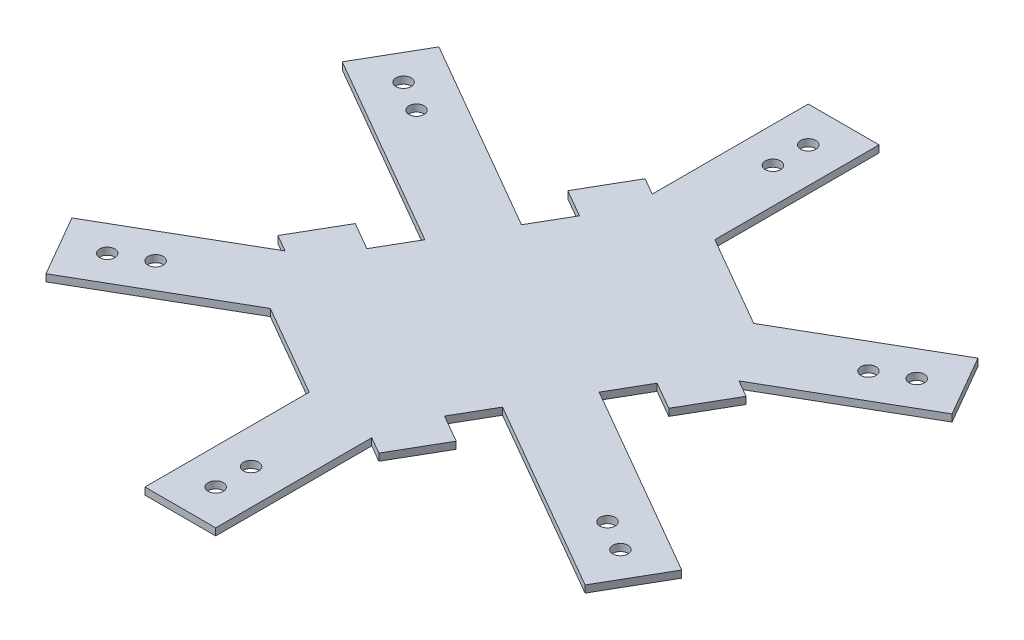
SolidWorks part; units mm, degrees
material "Thornel Mat VMA"
ref_plane "Front Plane" through (0, 0, 0) normal (0, 0, 1) x (1, 0, 0)
ref_plane "Top Plane" through (0, 0, 0) normal (0, 1, 0) x (1, 0, 0)
ref_plane "Right Plane" through (0, 0, 0) normal (1, 0, 0) x (0, 0, -1)
sketch "Sketch1" plane through (0, 0, 0) normal (0, 1, 0) x (1, 0, 0)
  line L0 (0, 88.7676) -> (0, -88.7676) construction
  line L1 (102.5, 0) -> (51.25, 88.7676)
  line L2 (51.25, 88.7676) -> (-51.25, 88.7676)
  line L3 (-51.25, 88.7676) -> (-102.5, 0)
  line L4 (-102.5, 0) -> (-51.25, -88.7676)
  line L5 (-51.25, -88.7676) -> (51.25, -88.7676)
  line L6 (51.25, -88.7676) -> (102.5, 0)
  line L7 (73.6325, 0) -> (36.8162, 63.7676)
  line L8 (-10, 63.7676) -> (-36.8162, 63.7676)
  line L9 (-36.8162, 63.7676) -> (-73.6325, 0)
  line L10 (-73.6325, 0) -> (-36.8162, -63.7676)
  line L11 (10, -63.7676) -> (36.8162, -63.7676)
  line L12 (36.8162, -63.7676) -> (73.6325, 0)
  line L17 (-25, -40.75) -> (25, 40.75) construction
  line L18 (-25, 40.75) -> (25, -40.75) construction
  line L19 (-10, 63.7676) -> (-10, 45.7676)
  line L20 (-10, 45.7676) -> (-30, 45.7676)
  line L21 (-30, -45.7676) -> (-30, 45.7676)
  line L22 (-30, 0) -> (25, 0) construction
  line L23 (-10, -45.7676) -> (-30, -45.7676)
  line L24 (-10, -63.7676) -> (-10, -45.7676)
  line L25 (10, -63.7676) -> (10, -45.7676)
  line L26 (10, -45.7676) -> (30, -45.7676)
  line L27 (30, -45.7676) -> (30, 45.7676)
  line L28 (10, 45.7676) -> (30, 45.7676)
  line L29 (10, 63.7676) -> (10, 45.7676)
  line L30 (-36.8162, -63.7676) -> (-10, -63.7676)
  line L31 (10, 63.7676) -> (36.8162, 63.7676)
  circle A0 centre (0, 0) radius 88.7676 construction
  circle A1 centre (0, 0) radius 63.7676 construction
  dimension "D1" = 205
  dimension "D2" = 25
  dimension "D3" = 81.5
  dimension "D4" = 50
  dimension "D5" = 18
  dimension "D6" = 10
  dimension "D7" = 20
extrude "Boss-Extrude2" add sketch "Sketch1" along normal blind 2
sketch "Sketch2" plane through (0, 2, 0) normal (0, 1, 0) x (1, 0, 0)
  line L0 (-55.2244, -31.8838) -> (-76.875, -44.3838) construction
  line L1 (-73.6325, 0) -> (-36.8162, -63.7676) construction
  line L2 (-102.5, 0) -> (-51.25, -88.7676) construction
  line L3 (-55.2244, -31.8838) -> (-63.8846, -36.8838) construction
  line L4 (-63.8846, -36.8838) -> (-72.5449, -41.8838) construction
  circle A0 centre (-72.5449, -41.8838) radius 2.15
  circle A1 centre (-63.8846, -36.8838) radius 2.15
  circle A2 centre (-72.5449, 41.8838) radius 2.15
  circle A3 centre (-63.8846, 36.8838) radius 2.15
  circle A4 centre (0, 83.7676) radius 2.15
  circle A5 centre (0, 73.7676) radius 2.15
  circle A6 centre (72.5449, 41.8838) radius 2.15
  circle A7 centre (63.8846, 36.8838) radius 2.15
  circle A8 centre (72.5449, -41.8838) radius 2.15
  circle A9 centre (63.8846, -36.8838) radius 2.15
  circle A10 centre (0, -83.7676) radius 2.15
  circle A11 centre (0, -73.7676) radius 2.15
  point P33 (0, 0)
  dimension "D3" = 4.3
  dimension "D4" = 4.3
  dimension "D1" = 10
  dimension "D2" = 10
  dimension "D5" = 6
extrude "Cut-Extrude1" cut sketch "Sketch2" against normal blind 10
sketch "Sketch7" plane through (0, 0, 0) normal (0, -1, 0) x (1, 0, 0)
  line L1 (73.6325, 0) -> (36.8162, 63.7676)
  line L2 (36.8162, 63.7676) -> (-36.8162, 63.7676)
  line L3 (-36.8162, 63.7676) -> (-73.6325, 0)
  line L4 (-73.6325, 0) -> (-36.8162, -63.7676)
  line L5 (-36.8162, -63.7676) -> (36.8162, -63.7676)
  line L6 (36.8162, -63.7676) -> (73.6325, 0)
  circle A0 centre (0, 0) radius 63.7676 construction
extrude "Cut-Extrude3" cut sketch "Sketch7" against normal blind 30
sketch "Sketch8" plane through (0, 0, 0) normal (0, -1, 0) x (1, 0, 0)
  line L0 (-36.8162, 63.7676) -> (36.8162, -63.7676) construction
  line L1 (0, 0) -> (-23, 39.8372) construction
  line L2 (-23, 39.8372) -> (2.9808, 54.8372) construction
  line L3 (55.2244, 31.8838) -> (0, 0) construction
  line L4 (36.8162, 63.7676) -> (73.6325, 0) construction
  line L5 (-48.9808, 24.8372) -> (2.9808, 54.8372)
  line L6 (2.9808, 54.8372) -> (48.9808, -24.8372)
  line L7 (25.9808, 15) -> (0, 0)
  line L8 (-23, 39.8372) -> (0, 0)
  line L9 (-48.9808, 24.8372) -> (-2.9808, -54.8372)
  line L10 (-2.9808, -54.8372) -> (48.9808, -24.8372)
  point P16 (-25.9808, -15)
  dimension "D1" = 46
  dimension "D3" = 30
  dimension "D4" = 90
extrude "Boss-Extrude4" add sketch "Sketch8" against normal blind 2 separate body contours L5 L8 L7 L6 | L9 L10 L6 L7 L8 L5
sketch "Sketch9" plane through (0, 0, 0) normal (0, -1, 0) x (-1, 0, 0)
  line L0 (55.2244, -31.8838) -> (50.2244, -40.5441) construction
  line L1 (73.6325, 0) -> (36.8162, -63.7676) construction
  line L2 (55.2244, -31.8838) -> (60.2244, -23.2235) construction
  line L3 (60.2244, -23.2235) -> (25.5833, -3.2235)
  line L4 (76.875, -44.3838) -> (55.2244, -31.8838) construction
  line L5 (102.5, 0) -> (51.25, -88.7676) construction
  line L6 (50.2244, -40.5441) -> (15.5833, -20.5441)
  line L7 (60.2244, -23.2235) -> (50.2244, -40.5441)
  line L8 (25.5833, -3.2235) -> (15.5833, -20.5441)
  line L9 (-10, -63.7676) -> (-10, -23.7676)
  line L10 (10, -63.7676) -> (-10, -63.7676)
  line L11 (10, -63.7676) -> (10, -23.7676)
  line L12 (10, -23.7676) -> (-10, -23.7676)
  line L13 (-60.2244, -23.2235) -> (-25.5833, -3.2235)
  line L14 (-50.2244, -40.5441) -> (-60.2244, -23.2235)
  line L15 (-50.2244, -40.5441) -> (-15.5833, -20.5441)
  line L16 (-15.5833, -20.5441) -> (-25.5833, -3.2235)
  line L17 (-50.2244, 40.5441) -> (-15.5833, 20.5441)
  line L18 (-60.2244, 23.2235) -> (-50.2244, 40.5441)
  line L19 (-60.2244, 23.2235) -> (-25.5833, 3.2235)
  line L20 (-25.5833, 3.2235) -> (-15.5833, 20.5441)
  line L21 (10, 63.7676) -> (10, 23.7676)
  line L22 (-10, 63.7676) -> (10, 63.7676)
  line L23 (-10, 63.7676) -> (-10, 23.7676)
  line L24 (-10, 23.7676) -> (10, 23.7676)
  line L25 (60.2244, 23.2235) -> (25.5833, 3.2235)
  line L26 (50.2244, 40.5441) -> (60.2244, 23.2235)
  line L27 (50.2244, 40.5441) -> (15.5833, 20.5441)
  line L28 (15.5833, 20.5441) -> (25.5833, 3.2235)
  point P33 (0, 0)
  dimension "D1" = 10
  dimension "D2" = 6
extrude "Boss-Extrude5" add sketch "Sketch9" against normal blind 2
sketch "Sketch10" plane through (0, 0, 0) normal (0, -1, 0) x (-1, 0, 0)
  line L0 (60.2244, -23.2235) -> (98.1153, -45.0999)
  line L1 (73.6325, 0) -> (60.2244, -23.2235) construction
  line L2 (60.2244, 23.2235) -> (103.941, 48.4634)
  line L3 (60.2244, 23.2235) -> (60.2244, -23.2235)
  line L4 (98.1153, -45.0999) -> (121.7836, 0)
  line L5 (121.7836, 0) -> (103.941, 48.4634)
  line L6 (10, -107.5202) -> (60.8918, -105.4677)
  line L7 (10, -63.7676) -> (10, -107.5202)
  line L8 (50.2244, -40.5441) -> (10, -63.7676)
  line L9 (50.2244, -40.5441) -> (93.941, -65.7839)
  line L10 (60.8918, -105.4677) -> (93.941, -65.7839)
  line L11 (-88.1153, -62.4204) -> (-60.8918, -105.4677)
  line L12 (-50.2244, -40.5441) -> (-88.1153, -62.4204)
  line L13 (-10, -63.7676) -> (-50.2244, -40.5441)
  line L14 (-10, -63.7676) -> (-10, -114.2472)
  line L15 (-60.8918, -105.4677) -> (-10, -114.2472)
  line L16 (-98.1153, 45.0999) -> (-121.7836, 0)
  line L17 (-60.2244, 23.2235) -> (-98.1153, 45.0999)
  line L18 (-60.2244, -23.2235) -> (-60.2244, 23.2235)
  line L19 (-60.2244, -23.2235) -> (-103.941, -48.4634)
  line L20 (-121.7836, 0) -> (-103.941, -48.4634)
  line L21 (-10, 107.5202) -> (-60.8918, 105.4677)
  line L22 (-10, 63.7676) -> (-10, 107.5202)
  line L23 (-50.2244, 40.5441) -> (-10, 63.7676)
  line L24 (-50.2244, 40.5441) -> (-93.941, 65.7839)
  line L25 (-60.8918, 105.4677) -> (-93.941, 65.7839)
  line L26 (88.1153, 62.4204) -> (60.8918, 105.4677)
  line L27 (50.2244, 40.5441) -> (88.1153, 62.4204)
  line L28 (10, 63.7676) -> (50.2244, 40.5441)
  line L29 (10, 63.7676) -> (10, 114.2472)
  line L30 (60.8918, 105.4677) -> (10, 114.2472)
  point P37 (0, 0)
  dimension "D1" = 90
  dimension "D2" = 6
extrude "Cut-Extrude4" cut sketch "Sketch10" against normal blind 2
sketch "Sketch12" plane through (0, 0, 0) normal (0, -1, 0) x (1, 0, 0)
  line L0 (-72.5449, -41.8838) -> (-81.2051, -46.8838) construction
  line L1 (-81.875, -35.7235) -> (-94.1895, -42.8333) construction
  line L3 (-81.2051, -46.8838) -> (-86.2051, -38.2235)
  line L4 (-86.2051, -38.2235) -> (-81.875, -35.7235)
  line L5 (-81.875, -35.7235) -> (-71.875, -53.0441)
  line L6 (-81.2051, -46.8838) -> (-76.2051, -55.5441)
  line L7 (-76.2051, -55.5441) -> (-71.875, -53.0441)
  line L8 (-81.2051, 46.8838) -> (-86.2051, 38.2235)
  line L9 (-86.2051, 38.2235) -> (-81.875, 35.7235)
  line L10 (-71.875, 53.0441) -> (-81.875, 35.7235)
  line L11 (-81.2051, 46.8838) -> (-76.2051, 55.5441)
  line L12 (-76.2051, 55.5441) -> (-71.875, 53.0441)
  line L13 (0, 93.7676) -> (-10, 93.7676)
  line L14 (-10, 93.7676) -> (-10, 88.7676)
  line L15 (10, 88.7676) -> (-10, 88.7676)
  line L16 (0, 93.7676) -> (10, 93.7676)
  line L17 (10, 93.7676) -> (10, 88.7676)
  line L18 (81.2051, 46.8838) -> (76.2051, 55.5441)
  line L19 (76.2051, 55.5441) -> (71.875, 53.0441)
  line L20 (81.875, 35.7235) -> (71.875, 53.0441)
  line L21 (81.2051, 46.8838) -> (86.2051, 38.2235)
  line L22 (86.2051, 38.2235) -> (81.875, 35.7235)
  line L23 (81.2051, -46.8838) -> (86.2051, -38.2235)
  line L24 (86.2051, -38.2235) -> (81.875, -35.7235)
  line L25 (71.875, -53.0441) -> (81.875, -35.7235)
  line L26 (81.2051, -46.8838) -> (76.2051, -55.5441)
  line L27 (76.2051, -55.5441) -> (71.875, -53.0441)
  line L28 (0, -93.7676) -> (10, -93.7676)
  line L29 (10, -93.7676) -> (10, -88.7676)
  line L30 (-10, -88.7676) -> (10, -88.7676)
  line L31 (0, -93.7676) -> (-10, -93.7676)
  line L32 (-10, -93.7676) -> (-10, -88.7676)
  point P38 (0, 0)
  dimension "D1" = 10
  dimension "D2" = 10
  dimension "D3" = 6
extrude "Boss-Extrude6" add sketch "Sketch12" against normal blind 2
sketch "Sketch13" plane through (0, 2, 0) normal (0, 1, 0) x (1, 0, 0)
  line L2 (0, 0) -> (23, 39.8372) construction
  line L3 (10, 47.3427) -> (36, 32.3316) construction
sketch "Sketch14" plane through (0, 2, 0) normal (0, 1, 0) x (1, 0, 0)
  line L0 (0, 0) -> (23, 39.8372) construction
  line L1 (0, 0) -> (15, 25.9808) construction
  line L2 (15, 25.9808) -> (-22.2391, 47.4808) construction
  line L3 (-81.2051, 46.8838) -> (81.2051, -46.8838) construction
  line L4 (-86.2051, 38.2235) -> (-76.2051, 55.5441) construction
  line L5 (86.2051, -38.2235) -> (76.2051, -55.5441) construction
  line L6 (-26.2391, 40.5526) -> (-18.2391, 54.409)
  line L7 (-26.2391, 40.5526) -> (48.2391, -2.4474)
  line L8 (-18.2391, 54.409) -> (56.2391, 11.409)
  line L9 (19, 32.909) -> (11, 19.0526)
  line L10 (-48.2391, 2.4474) -> (-56.2391, -11.409)
  line L11 (-48.2391, 2.4474) -> (26.2391, -40.5526)
  line L12 (-19, -32.909) -> (-11, -19.0526)
  line L13 (-56.2391, -11.409) -> (18.2391, -54.409)
  line L14 (26.2391, -40.5526) -> (18.2391, -54.409)
  line L15 (48.2391, -2.4474) -> (56.2391, 11.409)
  line M3 (-10, 93.7676) -> (-10, 42.6795)
  line M4 (-10, 42.6795) -> (-20.9808, 23.6603)
  line M8 (-30.9808, 6.3397) -> (-41.9615, -12.6795)
  line M9 (-41.9615, -12.6795) -> (-86.2051, -38.2235)
  line M15 (10, -93.7676) -> (10, -42.6795)
  line M16 (10, -42.6795) -> (20.9808, -23.6603)
  line M20 (30.9808, -6.3397) -> (41.9615, 12.6795)
  line M21 (41.9615, 12.6795) -> (86.2051, 38.2235)
  dimension "D1" = 30
  dimension "D2" = 43
  dimension "D4" = 8
extrude "Boss-Extrude7" add sketch "Sketch14" against normal blind 2 contours L8 L6 L7 M4 M3 | L7 L15 L8 M21 M20 | L14 L11 L13 M16 M15 | L10 L13 L11 M9 M8
sketch "Sketch15" plane through (0, 2, 0) normal (0, 1, 0) x (1, 0, 0)
  line L0 (-18.2391, 54.409) -> (-14.775, 52.409)
  line L1 (-18.2391, 54.409) -> (-10, 49.6521) construction
  line L2 (-14.775, 52.409) -> (-22.775, 38.5526)
  line L3 (-26.2391, 40.5526) -> (-14.9808, 34.0526) construction
  line L4 (-22.775, 38.5526) -> (-26.2391, 40.5526)
  line L5 (-26.2391, 40.5526) -> (-18.2391, 54.409)
  line L6 (23, 39.8372) -> (0, 0) construction
  line L7 (-81.2051, 46.8838) -> (0, 0) construction
  line L8 (-86.2051, 38.2235) -> (-76.2051, 55.5441) construction
  line L9 (-44.775, 0.4474) -> (-48.2391, 2.4474)
  line L10 (-52.775, -13.409) -> (-44.775, 0.4474)
  line L11 (-48.2391, 2.4474) -> (-56.2391, -11.409)
  line L12 (-56.2391, -11.409) -> (-52.775, -13.409)
  line L13 (18.2391, -54.409) -> (14.775, -52.409)
  line L14 (14.775, -52.409) -> (22.775, -38.5526)
  line L15 (26.2391, -40.5526) -> (18.2391, -54.409)
  line L16 (22.775, -38.5526) -> (26.2391, -40.5526)
  line L17 (44.775, -0.4474) -> (48.2391, -2.4474)
  line L18 (52.775, 13.409) -> (44.775, -0.4474)
  line L19 (48.2391, -2.4474) -> (56.2391, 11.409)
  line L20 (56.2391, 11.409) -> (52.775, 13.409)
  dimension "D1" = 4
extrude "Cut-Extrude5" cut sketch "Sketch15" against normal blind 2
